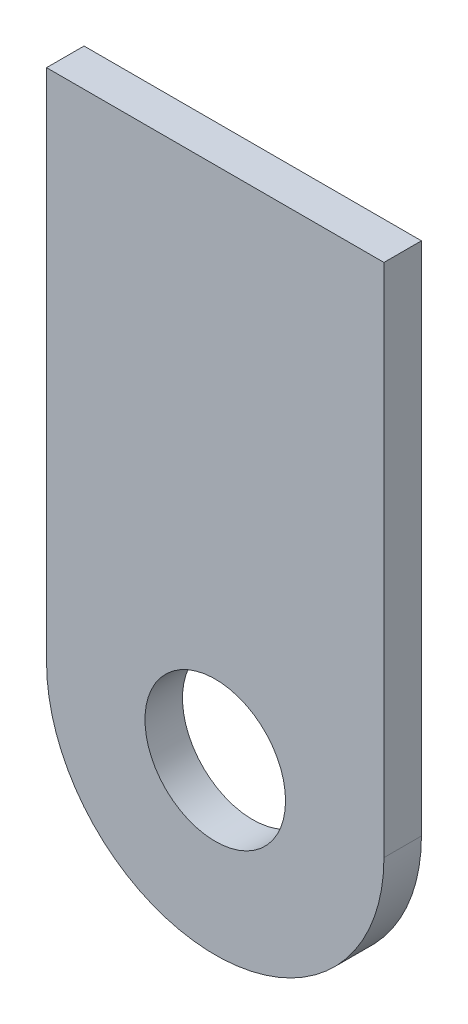
SolidWorks part; units mm, degrees
ref_plane "Front Plane" through (0, 0, 0) normal (0, 0, 1) x (1, 0, 0)
ref_plane "Top Plane" through (0, 0, 0) normal (0, 1, 0) x (1, 0, 0)
ref_plane "Right Plane" through (0, 0, 0) normal (1, 0, 0) x (0, 0, -1)
sketch "Sketch1" plane through (0, 0, 0) normal (0, 0, 1) x (1, 0, 0)
  line L1 (-11.43, -34.925) -> (11.43, -34.925)
  line L2 (-11.43, -34.925) -> (-11.43, 34.925)
  line L3 (-11.43, 34.925) -> (11.43, 34.925)
  line L4 (11.43, -34.925) -> (11.43, 34.925)
  line L5 (-11.43, -34.925) -> (11.43, 34.925) construction
  line L6 (-11.43, 34.925) -> (11.43, -34.925) construction
  circle A0 centre (0, 0) radius 11.43
  circle A1 centre (0, 0) radius 4.7625
  circle A2 centre (0, 34.925) radius 12.7
extrude "Boss-Extrude1" add sketch "Sketch1" along normal blind 2.54 contours L2 A2 L4 L3 | A2 L2 A0 L4 | A0 A1
